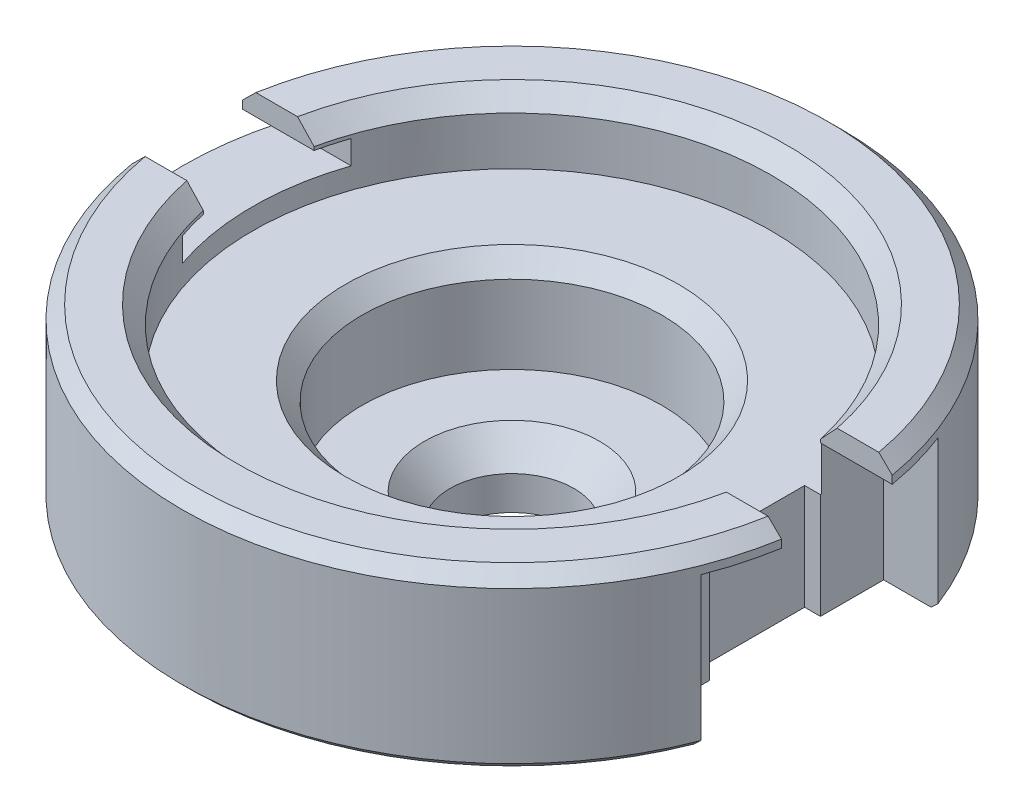
SolidWorks part; units mm, degrees
ref_plane "Alzado" through (0, 0, 0) normal (0, 0, 1) x (1, 0, 0)
ref_plane "Planta" through (0, 0, 0) normal (0, 1, 0) x (1, 0, 0)
ref_plane "Vista lateral" through (0, 0, 0) normal (1, 0, 0) x (0, 0, -1)
sketch "Sketch1" plane through (0, 0, 0) normal (0, 0, 1) x (1, 0, 0)
  line L0 (0.3324, 0.2343) -> (0.235, 0.128)
  line L1 (0.235, 0.128) -> (0.235, 0)
  line L2 (0.235, 0) -> (0.304, 0)
  line L3 (0.304, 0) -> (0.4414, 0.15)
  line L4 (0.4414, 0.15) -> (0.825, 0.15)
  line L5 (0.825, 0.15) -> (0.85, 0.175)
  line L6 (0.85, 0.175) -> (0.85, 0.2)
  line L7 (0.85, 0.2) -> (1.225, 0.2)
  line L8 (1.225, 0.2) -> (1.25, 0.225)
  line L9 (1.25, 0.225) -> (1.25, 0.8)
  line L10 (1.25, 0.8) -> (1.2, 0.85)
  line L11 (1.2, 0.85) -> (1.0447, 0.85)
  line L12 (1.0447, 0.85) -> (0.9834, 0.7831)
  line L13 (0.9834, 0.7831) -> (0.9834, 0.6)
  line L14 (0.9834, 0.6) -> (0.632, 0.6)
  line L15 (0.632, 0.6) -> (0.5686, 0.5307)
  line L16 (0.5686, 0.5307) -> (0.5686, 0.2343)
  line L17 (0.5686, 0.2343) -> (0.3324, 0.2343)
  line L18 (0, 0.85) -> (0, 0) construction
  dimension "D1" = 0.235
  dimension "D2" = 0.304
  dimension "D3" = 0.3324
  dimension "D4" = 0.4414
  dimension "D5" = 0.5686
  dimension "D6" = 0.632
  dimension "D7" = 0.825
  dimension "D8" = 0.85
  dimension "D9" = 0.9834
  dimension "D10" = 1.0447
  dimension "D11" = 1.2
  dimension "D12" = 1.225
  dimension "D13" = 1.25
  dimension "D14" = 0.128
  dimension "D15" = 0.15
  dimension "D16" = 0.175
  dimension "D17" = 0.2
  dimension "D18" = 0.225
  dimension "D19" = 0.2343
  dimension "D20" = 0.5307
  dimension "D21" = 0.6
  dimension "D22" = 0.7831
  dimension "D23" = 0.8
  dimension "D24" = 0.85
revolve "Revolve1" add sketch "Sketch1" angle 360 about L18
sketch "Sketch2" plane through (0, 0, 0) normal (1, 0, 0) x (0, 0, -1)
  line L0 (1.2, 0.85) -> (-1.2, 0.85) construction
  line L1 (1.2, 0.85) -> (-1.2, 0.85) construction
  line L2 (0.9834, 0.6) -> (-0.9834, 0.6) construction
  line L3 (0.9834, 0.6) -> (-0.9834, 0.6) construction
  line L4 (0, -1000) -> (0, 49000) construction
  line L5 (0.21, -999.9776) -> (0.21, 49000.0224) construction
  line L6 (0.32, -999.9449) -> (0.32, 49000.0551) construction
  line L7 (-1000.7777, 0.68) -> (48999.2223, 0.68) construction
  line L8 (-999.1378, 0.77) -> (49000.8622, 0.77) construction
  line L9 (0.21, 0.9123) -> (0.21, 0.77)
  line L10 (0.21, 0.77) -> (0.32, 0.77)
  line L11 (0.32, 0.77) -> (0.32, 0.68)
  line L12 (0.32, 0.68) -> (-0.32, 0.68)
  line L13 (0.21, 0.9123) -> (-0.21, 0.9123)
  line L14 (-0.32, 0.77) -> (-0.32, 0.68)
  line L15 (-0.21, 0.77) -> (-0.32, 0.77)
  line L16 (-0.21, 0.9123) -> (-0.21, 0.77)
  point P22 (0, 0.68)
  point P25 (0, 0.9123)
  dimension "D1" = 0.21
  dimension "D2" = 0.32
  dimension "D3" = 0.08
  dimension "D4" = 0.09
extrude "Cut-Extrude1" cut sketch "Sketch2" against normal up to next
sketch "Sketch4" plane through (0, 0.85, 0) normal (0, 1, 0) x (1, 0, 0)
  line L0 (-1.1815, 0.21) -> (-1.0234, 0.21) construction
  line L1 (-1.1815, 0.21) -> (-1.0234, 0.21) construction
  line L2 (-1.0234, -0.21) -> (-1.1815, -0.21) construction
  line L3 (-1.0234, -0.21) -> (-1.1815, -0.21) construction
  line L4 (-1001.1452, 0.21) -> (48998.8548, 0.21) construction
  line L5 (-1001.1308, -0.21) -> (48998.8692, -0.21) construction
  line L6 (0, -1000) -> (0, 49000) construction
  line L7 (0.9, 0.21) -> (1.4797, 0.21)
  line L8 (0.9, 0.21) -> (0.9, -0.21)
  line L9 (0.9, -0.21) -> (1.4797, -0.21)
  line L10 (1.4797, 0.21) -> (1.4797, -0.21)
  dimension "D1" = 0.9
extrude "Cut-Extrude3" cut sketch "Sketch4" against normal up to next
sketch "Sketch5" plane through (0, 0, 0) normal (0, 1, 0) x (1, 0, 0)
  line L0 (0, -1000) -> (0, 49000) construction
  line L1 (0.96, -1000.0364) -> (0.96, 48999.9636) construction
  line L2 (-1000, 0) -> (49000, 0) construction
  line L3 (-999.8567, 0.45) -> (49000.1433, 0.45) construction
  line L4 (-999.7536, -0.45) -> (49000.2464, -0.45) construction
  line L6 (0.96, 0.45) -> (1.5537, 0.45)
  line L7 (0.96, 0.45) -> (0.96, -0.45)
  line L8 (0.96, -0.45) -> (1.5537, -0.45)
  line L9 (1.5537, 0.45) -> (1.5537, -0.45)
  dimension "D1" = 0.96
  dimension "D2" = 0.45
  dimension "D3" = 0.45
extrude "Cut-Extrude4" cut sketch "Sketch5" along normal blind 0.77
